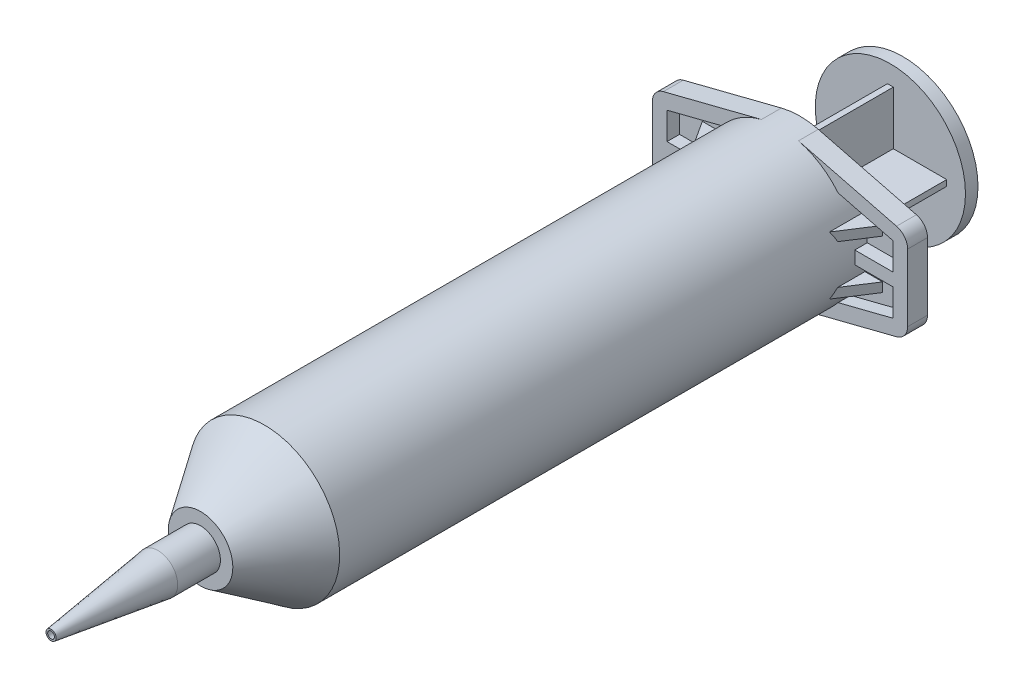
SolidWorks part; units mm, degrees
ref_plane "Front Plane" through (0, 0, 0) normal (0, 0, 1) x (1, 0, 0)
ref_plane "Top Plane" through (0, 0, 0) normal (0, 1, 0) x (1, 0, 0)
ref_plane "Right Plane" through (0, 0, 0) normal (1, 0, 0) x (0, 0, -1)
sketch "Sketch1" plane through (0, 0, 0) normal (1, 0, 0) x (0, 0, -1)
  line L0 (-73.4695, 0) -> (73.4695, 0) construction
  line L1 (52.2605, 11.43) -> (52.2605, -11.43) construction
  line L2 (52.2605, 12.954) -> (52.2605, -12.954) construction
  line L3 (-73.4695, 0.5842) -> (-73.4695, -0.5842) construction
  point P0 (55.6895, 0)
  point P3 (-25.527, 0)
  point P4 (0, 0)
  point P6 (52.2605, 0)
  point P7 (-36.6395, 0)
  point P11 (52.2605, 0)
  point P14 (52.2605, 0)
  point P16 (-73.4695, 0)
  point P17 (-55.0545, 0)
  dimension "Barrel ID" = 22.86
  dimension "Barrel OD" = 25.908
  dimension "Base Thickness" = 3.429
  dimension "Barrel Length" = 88.9
  dimension "Tip Length" = 36.83
  dimension "Tip Taper Length" = 18.415
  dimension "Tip ID" = 1.1684
  dimension "D1" = 11.1125
  dimension "D2" = 17.78
sketch "Sketch2" plane through (0, 0, 0) normal (1, 0, 0) x (0, 0, -1)
  line L0 (52.2605, 11.43) -> (-36.6395, 11.43)
  line L1 (-36.6395, 11.43) -> (-46.2804, 4.9872)
  line L2 (-46.2804, 4.9872) -> (-46.2804, 3.1369)
  line L4 (-55.0545, 3.429) -> (-73.4695, 0.8763)
  line L5 (-73.4695, 0.8763) -> (-73.4695, 0.5842)
  line L6 (-73.4695, 0.5842) -> (-55.0545, 3.1369)
  line L8 (-47.6885, 3.429) -> (-47.6885, 5.5702)
  line L9 (-47.6885, 5.5702) -> (-36.6395, 12.954)
  line L10 (-36.6395, 12.954) -> (52.2605, 12.954)
  line L11 (52.2605, 12.954) -> (52.2605, 11.43)
  line L12 (-73.4695, -0.5842) -> (-73.4695, 0.5842) construction
  line L13 (-36.6395, 11.43) -> (-36.6395, 0) construction
  line L14 (-55.0545, 3.1369) -> (-55.0545, 3.429) construction
  line L15 (-47.6885, -5.5702) -> (-47.6885, 5.5702) construction
  line L16 (-36.6395, 12.954) -> (-36.6395, 11.43) construction
  line L17 (-46.2804, 4.9872) -> (-47.6885, 5.5702) construction
  line L18 (-47.6885, 3.429) -> (-55.0545, 3.429)
  line L19 (-46.2804, 3.1369) -> (-55.0545, 3.1369)
  line L20 (-73.4695, 0) -> (73.4695, 0) construction
  line L21 (-73.4695, 0) -> (73.4695, 0) construction
  line L22 (-73.4695, -0.8763) -> (-73.4695, 0.8763) construction
  line L23 (-47.6885, -3.429) -> (-47.6885, 3.429) construction
  point P20 (-47.6885, 0)
  point P21 (-36.6395, 0)
  point P26 (-73.4695, 0)
  point P30 (-47.6885, 0)
  point P40 (-73.4695, 0)
  dimension "D4" = 11.049
  dimension "D2" = 11.1404
  dimension "D1" = 1.7526
  dimension "Tip Diameter at Barrel" = 6.858
revolve "Revolve1" add sketch "Sketch2" angle 360 about L0
sketch "Sketch3" plane through (0, 0, -52.2605) normal (0, 0, -1) x (-1, 0, 0)
  line L0 (-22.0218, 0) -> (22.0218, 0) construction
  line L1 (-3.1887, 12.5554) -> (-22.0218, 7.7724)
  line L2 (-3.1887, -12.5554) -> (-22.0218, -7.7724)
  line L3 (3.1887, -12.5554) -> (22.0218, -7.7724)
  line L4 (3.1887, 12.5554) -> (22.0218, 7.7724)
  line L5 (-22.0218, 7.7724) -> (22.0218, 7.7724) construction
  line L6 (-22.0218, -7.7724) -> (22.0218, -7.7724) construction
  line L7 (-22.0218, 7.7724) -> (-22.0218, -7.7724)
  line L8 (-3.1887, 12.5554) -> (-3.1887, -12.5554) construction
  line L9 (3.1887, 12.5554) -> (3.1887, -12.5554) construction
  line L10 (22.0218, 7.7724) -> (22.0218, -7.7724)
  circle A1 centre (0, 0) radius 12.954 construction
  circle A7 centre (0, 0) radius 11.43 construction
  circle A8 centre (0, 0) radius 11.43
  arc A9 (3.1887, 12.5554) -> (-3.1887, 12.5554) centre (0, 0) ccw
  arc A10 (3.1887, -12.5554) -> (-3.1887, -12.5554) centre (0, 0) cw
  point P6 (0, 0)
  dimension "D4" = 25.908
  dimension "D1" = 44.0436
  dimension "D2" = 15.5448
extrude "Boss-Extrude1" add sketch "Sketch3" along normal up to vertex (3.429 mm away) up to point (0, 0, -55.6895)
fillet "Fillet1" radius 2.54 4 edges at (-22.0218, -7.7724, -53.975) (-22.0218, 7.7724, -53.975) (22.0218, -7.7724, -53.975) (22.0218, 7.7724, -53.975)
ref_plane "Plane1" through (0, 0, -73.4695) normal (0, 0, 1) x (1, 0, 0)
sketch "Sketch5" plane through (0, 0, -73.4695) normal (0, 0, 1) x (1, 0, 0)
  circle A0 centre (0, 0) radius 12.954
  dimension "D1" = 25.908
extrude "Boss-Extrude2" add sketch "Sketch5" along normal blind 2.159 separate body
sketch "Sketch6" plane through (0, 0, -71.3105) normal (0, 0, 1) x (1, 0, 0)
  line L0 (0, -9.7155) -> (0, 9.7155) construction
  line L1 (0, 11.43) -> (0, -11.43) construction
  line L2 (-9.7155, 0) -> (9.7155, 0) construction
  line L3 (-0.508, 9.7155) -> (0.508, 9.7155)
  line L4 (9.7155, -0.508) -> (9.7155, 0.508)
  line L5 (-9.7155, -0.508) -> (-9.7155, 0.508)
  line L6 (-0.508, -9.7155) -> (0.508, -9.7155)
  line L7 (0.508, 9.7155) -> (0.508, 0.508)
  line L8 (9.7155, 0.508) -> (0.508, 0.508)
  line L9 (9.7155, -0.508) -> (0.508, -0.508)
  line L10 (0.508, -9.7155) -> (0.508, -0.508)
  line L11 (-0.508, -9.7155) -> (-0.508, -0.508)
  line L12 (-9.7155, -0.508) -> (-0.508, -0.508)
  line L13 (-0.508, 9.7155) -> (-0.508, 0.508)
  line L14 (-9.7155, 0.508) -> (-0.508, 0.508)
  point P6 (0, 0)
  point P10 (0, 0)
  point P13 (0, 9.7155)
  point P16 (9.7155, 0)
  point P19 (-9.7155, 0)
  point P22 (0, -9.7155)
  dimension "D1" = 19.431
  dimension "D2" = 1.016
extrude "Boss-Extrude3" add sketch "Sketch6" along normal up to vertex (96.8375 mm away) up to point (0, 0, 25.527)
sketch "Sketch7" plane through (0, 0, 25.527) normal (0, 0, 1) x (1, 0, 0)
  circle A0 centre (0, 0) radius 10.287
  dimension "D1" = 20.574
extrude "Boss-Extrude4" add sketch "Sketch7" along normal blind 1.27
sketch "Sketch8" plane through (0, 0, 0) normal (1, 0, 0) x (0, 0, -1)
  line L0 (-26.797, 10.287) -> (-26.797, -10.287) construction
  line L1 (-26.797, 10.287) -> (-26.797, -10.287) construction
  line L2 (-73.4695, 0) -> (73.4695, 0) construction
  line L3 (-73.4695, 0) -> (73.4695, 0) construction
  line L4 (-26.797, -11.43) -> (-26.797, 11.43) construction
  line L8 (-36.6395, 0) -> (-26.797, 0)
  line L11 (-31.2261, 11.43) -> (-28.2734, 11.43) construction
  line L12 (-32.7025, 11.43) -> (-31.2261, 11.43) construction
  line L13 (-26.797, 11.43) -> (-28.2734, 11.43) construction
  line L14 (-26.797, 10.287) -> (-28.2734, 10.287)
  line L15 (-36.6395, 0) -> (-36.6395, 11.43) construction
  line L16 (-36.6395, 11.43) -> (-32.7025, 11.43) construction
  line L17 (-28.2734, 10.287) -> (-29.7497, 11.43)
  line L18 (-29.7497, 11.43) -> (-31.2261, 10.287)
  line L19 (-31.2261, 10.287) -> (-32.7025, 10.287)
  line L20 (-32.7025, 10.287) -> (-34.1789, 11.43)
  line L21 (-34.1789, 11.43) -> (-36.6395, 0)
  line L22 (-32.7025, 11.43) -> (-32.7025, 10.287) construction
  line L23 (-31.2261, 11.43) -> (-31.2261, 10.287) construction
  line L24 (-28.2734, 11.43) -> (-28.2734, 10.287) construction
  line L25 (-28.2734, 10.287) -> (-31.2261, 10.287) construction
  line L26 (-26.797, 10.287) -> (-26.797, 0)
  point P4 (-26.797, 0)
  point P8 (-26.797, 0)
  dimension "D1" = 22.86
  dimension "D3" = 1.4764
  dimension "D2" = 9.8425
  dimension "D4" = 2.9527
revolve "Revolve2" add sketch "Sketch8" angle 360 about L3
sketch "Sketch12" plane through (0, 0, -52.2605) normal (0, 0, 1) x (1, 0, 0)
  line L6 (19.4818, 5.7968) -> (10.0306, 8.1972)
  line L7 (19.4818, -5.7968) -> (10.0306, -8.1972)
  line L8 (19.4818, -1.1049) -> (19.4818, 1.1049) construction
  line L9 (19.4818, -5.7968) -> (2.5634, -10.0936)
  line L10 (19.4818, 5.7968) -> (19.4818, -5.7968)
  line L11 (2.5634, 10.0936) -> (19.4818, 5.7968)
  line L12 (19.4818, -5.7968) -> (2.5634, -10.0936) construction
  line L13 (19.4818, 5.7968) -> (19.4818, -5.7968) construction
  line L14 (2.5634, 10.0936) -> (19.4818, 5.7968) construction
  line L15 (19.4818, 1.1049) -> (12.9068, 1.1049)
  line L16 (19.4818, -1.1049) -> (12.9068, -1.1049)
  line L17 (19.4818, 1.1049) -> (19.4818, 5.7968)
  line L18 (19.4818, -1.1049) -> (19.4818, -5.7968)
  arc A4 (3.1887, -12.5554) -> (3.1887, 12.5554) centre (0, 0) ccw construction
  arc A5 (3.1887, -12.5554) -> (3.1887, 12.5554) centre (0, 0) ccw construction
  arc A7 (12.9068, 1.1049) -> (10.0306, 8.1972) centre (0, 0) ccw
  arc A8 (12.9068, -1.1049) -> (10.0306, -8.1972) centre (0, 0) cw
  point P13 (19.4818, 0)
  dimension "D2" = 2.2098
  dimension "D1" = 2.54
extrude "Cut-Extrude1" cut sketch "Sketch12" against normal blind 2.159
sketch "Sketch14" plane through (0, 0, 0) normal (0, 1, 0) x (1, 0, 0)
  line L0 (12.9068, 54.4195) -> (19.4818, 54.4195) construction
  line L1 (12.9068, 54.4195) -> (19.4818, 54.4195) construction
  line L2 (11.43, 55.6895) -> (-11.43, 55.6895) construction
  line L3 (11.43, 55.6895) -> (-11.43, 55.6895) construction
  line L4 (12.9068, 54.4195) -> (11.43, 54.4195) construction
  line L5 (11.43, 55.6895) -> (11.43, 54.4195) construction
  line L6 (11.43, 54.4195) -> (11.43, 48.0695)
  line L7 (11.43, 48.0695) -> (15.5448, 54.4195)
  line L8 (11.43, 54.4195) -> (15.5448, 54.4195)
  dimension "D1" = 3.937
  dimension "D2" = 6.35
extrude "Boss-Extrude5" add sketch "Sketch14" along normal mid plane 10.033
sketch "Sketch15" plane through (0, 0, -54.4195) normal (0, 0, 1) x (1, 0, 0)
  line L0 (15.5448, -1.1049) -> (15.5448, -5.0165) construction
  line L1 (15.5448, 5.0165) -> (15.5448, 1.1049) construction
  line L2 (15.5448, -1.1049) -> (15.5448, -5.0165) construction
  line L3 (15.5448, 5.0165) -> (15.5448, 1.1049) construction
  line L4 (15.5448, 3.4163) -> (12.4954, 3.4163)
  line L5 (15.5448, -3.4163) -> (12.4954, -3.4163)
  line L6 (15.5448, 3.4163) -> (15.5448, 1.1049)
  line L7 (15.5448, -3.4163) -> (15.5448, -1.1049)
  line L8 (15.5448, -1.1049) -> (14.1458, -1.1049)
  line L10 (14.1458, 1.1049) -> (15.5448, 1.1049)
  line L11 (14.1458, 1.1049) -> (12.9068, 1.1049)
  line L12 (14.1458, -1.1049) -> (12.9068, -1.1049)
  arc A3 (12.4954, 3.4163) -> (12.9068, 1.1049) centre (0, 0) cw
  arc A4 (12.9068, -1.1049) -> (12.4954, -3.4163) centre (0, 0) cw
  circle A5 centre (0, 0) radius 12.954 construction
  dimension "D3" = 25.908
  dimension "D1" = 1.6002
  dimension "D2" = 1.6002
extrude "Cut-Extrude2" cut sketch "Sketch15" along normal through all
sketch "Sketch16" plane through (0, 0, -52.2605) normal (0, 0, 1) x (1, 0, 0)
  line L0 (14.1458, -1.1049) -> (12.9068, -1.1049) construction
  line L1 (14.1458, -1.1049) -> (14.1458, 1.1049) construction
  line L2 (12.9068, 1.1049) -> (14.1458, 1.1049) construction
  line L3 (14.1458, -1.1049) -> (12.9068, -1.1049)
  line L4 (14.1458, -1.1049) -> (14.1458, 1.1049)
  line L5 (12.9068, 1.1049) -> (14.1458, 1.1049)
  arc A0 (12.9068, -1.1049) -> (12.9068, 1.1049) centre (0, 0) ccw construction
  arc A1 (12.9068, -1.1049) -> (12.9068, 1.1049) centre (0, 0) ccw
extrude "Cut-Extrude3" cut sketch "Sketch16" along normal through all
mirror "Mirror1" about plane through (0, 0, 0) normal (1, 0, 0) of "Cut-Extrude3", "Cut-Extrude1", "Boss-Extrude5", "Cut-Extrude2"
sketch "Sketch9" plane through (0, 0, 0) normal (1, 0, 0) x (0, 0, -1)
  line L0 (-36.6395, 0) -> (-36.6395, 12.954) construction
  line L1 (-36.6395, 0) -> (-36.6395, -12.954) construction
  line L2 (52.2605, 0) -> (52.2605, 12.954) construction
  line L3 (52.2605, 11.43) -> (52.2605, -11.43) construction
  line L4 (52.2605, 0) -> (52.2605, -12.954) construction
  point P0 (-36.6395, -12.954)
  point P1 (52.2605, -12.954)
  point P3 (-36.6395, 12.954)
  point P5 (52.2605, 12.954)
sketch "Sketch10" plane through (0, 0, 0) normal (0, 0, 1) x (1, 0, 0)
  line L0 (-0.5842, 0) -> (0.5842, 0)
  line L2 (-12.954, 0) -> (12.954, 0)
  point P6 (0, 0)
  point P7 (-0.5842, 0)
  point P9 (0.5842, 0)
  point P12 (0, 0)
  point P13 (-12.954, 0)
  point P14 (12.954, 0)
  dimension "D1" = 1.1684
  dimension "D2" = 25.908
sketch "Sketch11" plane through (0, 0, 0) normal (0, 0, 1) x (1, 0, 0)
  line L0 (11.43, 0) -> (-11.43, 0) construction
  circle A0 centre (0, 0) radius 11.43
  point P5 (0, 0)
  point P7 (11.43, 0)
  point P8 (-11.43, 0)
  dimension "D1" = 22.86
equation "\"D1@Sketch8\"=\"Barrel ID@sketch1\""
equation "\"D3@Sketch8\"=\"D2@Sketch8\"*.15"
equation "\"D1@Sketch10\"=\"Tip ID@sketch1\""
equation "\"D2@Sketch10\"=\"Barrel OD@sketch1\""
equation "\"D1@Sketch11\"=\"Barrel ID@sketch1\""
equation "\"Tip Taper Length@Sketch1\"=\"Tip Length@Sketch1\"*.5"
equation "\"D1@Sketch2\" = \"Tip ID@Sketch1\" * 1.5"
equation "\"D2@Sketch2\"=\"Barrel OD@Sketch1\" * .43"
equation "\"D4@Sketch2\"=\"Tip Length@sketch1\"*.3"
equation "\"D1@Sketch1\"=\"Barrel Length@Sketch1\" * .125"
equation "\"D2@Sketch1\"=\"Barrel Length@Sketch1\"*.2"
equation "\"D4@Sketch3\"=\"Barrel OD@sketch1\""
equation "\"D2@Sketch3\"=\"D4@Sketch3\"*.6"
equation "\"D1@Sketch5\"=\"Barrel OD@sketch1\""
equation "\"D1@Sketch6\"=\"Barrel ID@Sketch1\" * .85"
equation "\"D1@Sketch7\"=\"Barrel ID@sketch1\"*.9"
equation "\"D4@Sketch8\"=\"D3@Sketch8\"*2"
equation "\"D3@Sketch15\"=\"Barrel OD@sketch1\""
